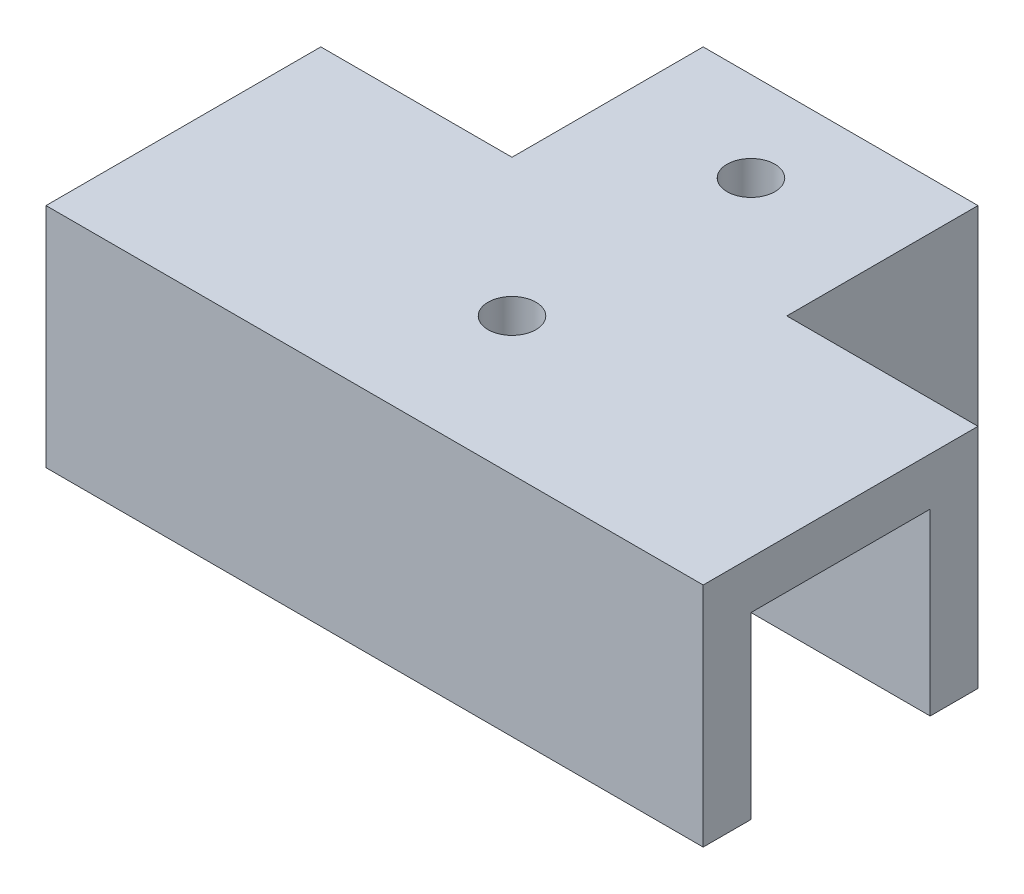
SolidWorks part; units mm, degrees
ref_plane "前视基准面" through (0, 0, 0) normal (0, 0, 1) x (1, 0, 0)
ref_plane "上视基准面" through (0, 0, 0) normal (0, 1, 0) x (1, 0, 0)
ref_plane "右视基准面" through (0, 0, 0) normal (1, 0, 0) x (0, 0, -1)
sketch "草图1" plane through (0, 0, 0) normal (0, 1, 0) x (1, 0, 0)
  line L1 (-29.4286, -3.1786) -> (25.5714, -3.1786)
  line L2 (-29.4286, -3.1786) -> (-29.4286, -7.1786)
  line L3 (-29.4286, -7.1786) -> (25.5714, -7.1786)
  line L4 (25.5714, -3.1786) -> (25.5714, -7.1786)
  line L5 (-29.4286, 15.8214) -> (-13.4286, 15.8214)
  line L6 (-29.4286, 15.8214) -> (-29.4286, 11.8214)
  line L7 (-29.4286, 11.8214) -> (-9.4286, 11.8214)
  line L8 (-9.4286, 15.8214) -> (-9.4286, 11.8214)
  line L9 (-9.4286, 11.8214) -> (-11.4286, 11.8214)
  line L10 (-9.4286, 11.8214) -> (-9.4286, 31.8214)
  line L11 (-9.4286, 31.8214) -> (-13.4286, 31.8214)
  line L12 (-13.4286, 15.8214) -> (-13.4286, 31.8214)
  line L13 (5.5714, 31.8214) -> (9.5714, 31.8214)
  line L14 (5.5714, 31.8214) -> (5.5714, 11.8214)
  line L15 (5.5714, 11.8214) -> (14.2143, 11.8214)
  line L16 (9.5714, 31.8214) -> (9.5714, 15.8214)
  line L17 (5.5714, 11.8214) -> (25.5714, 11.8214)
  line L18 (5.5714, 11.8214) -> (5.5714, 15.8214)
  line L19 (9.5714, 15.8214) -> (25.5714, 15.8214)
  line L20 (25.5714, 11.8214) -> (25.5714, 15.8214)
  dimension "D1" = 4
  dimension "D2" = 4
  dimension "D3" = 4
  dimension "D4" = 4
  dimension "D5" = 4
  dimension "D6" = 15
  dimension "D7" = 15
  dimension "D8" = 15
  dimension "D9" = 20
  dimension "D10" = 20
  dimension "D11" = 0
  dimension "D12" = 0
  dimension "D13" = 20
  dimension "D14" = 20
extrude "凸台-拉伸1" add sketch "草图1" along normal blind 15 contours L12 L5 L6 L7 L8 L10 L11 | L17 L20 L19 L16 L13 L14 L15 | L4 L1 L2 L3
sketch "草图2" plane through (0, 15, 0) normal (0, 1, 0) x (1, 0, 0)
  line L1 (-29.4286, 15.8214) -> (25.5714, 15.8214)
  line L2 (-29.4286, 15.8214) -> (-29.4286, -7.1786)
  line L3 (-29.4286, -7.1786) -> (25.5714, -7.1786)
  line L4 (25.5714, 15.8214) -> (25.5714, -7.1786)
  line L5 (-13.4286, 31.8214) -> (9.5714, 31.8214)
  line L6 (-13.4286, 31.8214) -> (-13.4286, 15.8214)
  line L7 (-13.4286, 15.8214) -> (9.5714, 15.8214)
  line L8 (9.5714, 31.8214) -> (9.5714, 15.8214)
extrude "凸台-拉伸2" add sketch "草图2" along normal blind 4 contours L4 L1 L2 L3 | L5 L2 L3 L4 | L8 L5 L6 L1
sketch "草图3" plane through (0, 19, 0) normal (0, 1, 0) x (1, 0, 0)
  line L0 (-13.4286, 31.8214) -> (9.5714, 31.8214) construction
  circle A0 centre (-1.9286, 24.3214) radius 2
  circle A1 centre (-1.9286, 4.3214) radius 2
  dimension "D1" = 7.5
  dimension "D2" = 4
  dimension "D3" = 4
extrude "切除-拉伸1" cut sketch "草图3" against normal blind 4
